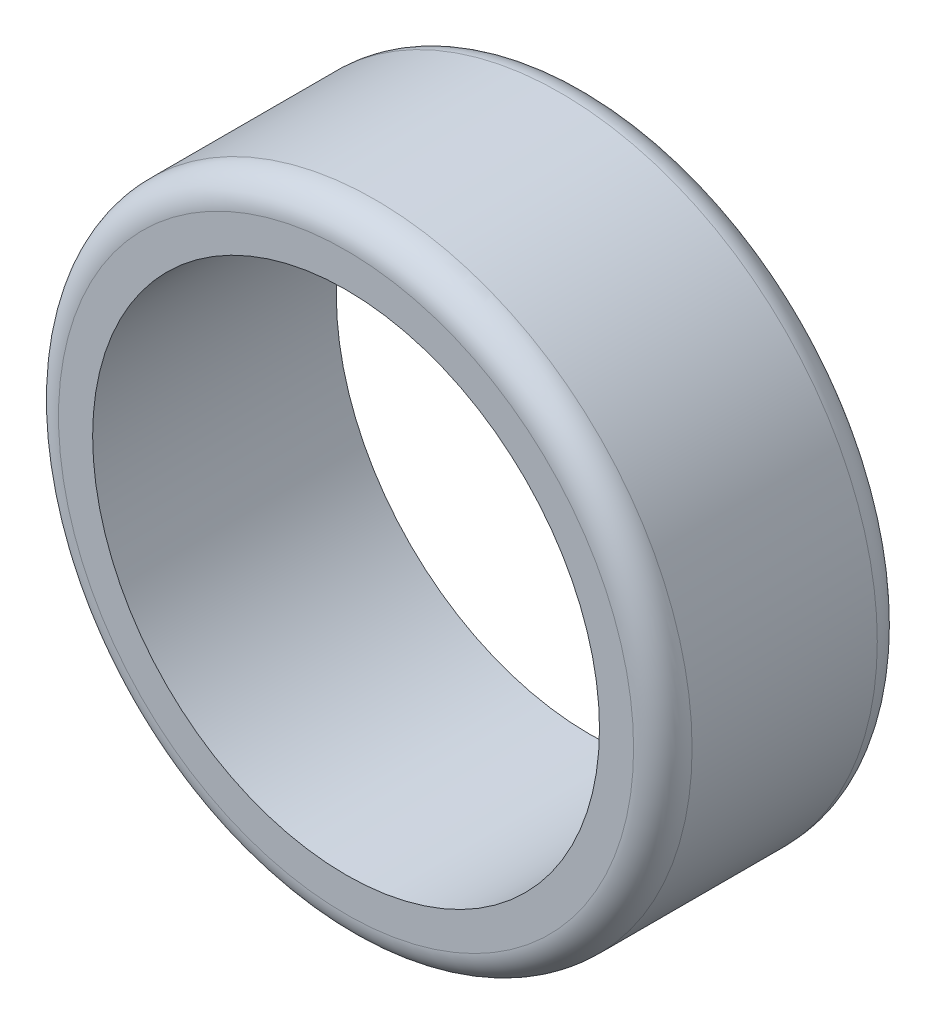
SolidWorks part; units mm, degrees
ref_plane "Front Plane" through (0, 0, 0) normal (0, 0, 1) x (1, 0, 0)
ref_plane "Top Plane" through (0, 0, 0) normal (0, 1, 0) x (1, 0, 0)
ref_plane "Right Plane" through (0, 0, 0) normal (1, 0, 0) x (0, 0, -1)
sketch "Sketch1" plane through (0, 0, 0) normal (0, 0, 1) x (1, 0, 0)
  circle A0 centre (0, 0) radius 32.5
  circle A1 centre (0, 0) radius 26
extrude "Boss-Extrude1" add sketch "Sketch1" along normal mid plane 25
fillet "Fillet1" radius 3 2 edges at (32.5, 0, -12.5) (32.5, 0, 12.5)
